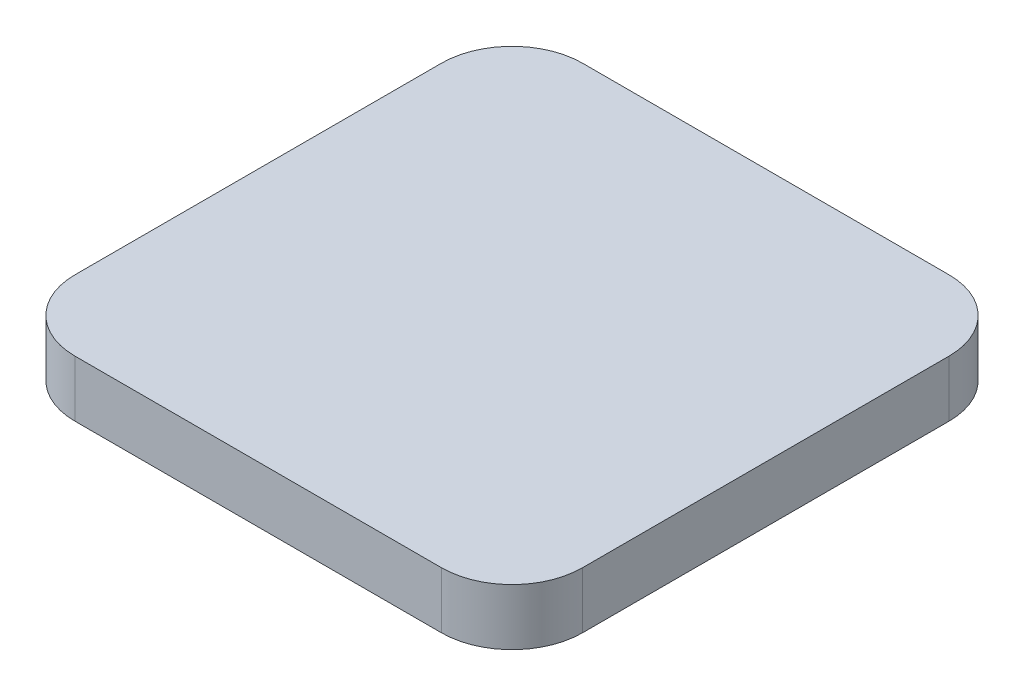
SolidWorks part; units mm, degrees
ref_plane "Front Plane" through (0, 0, 0) normal (0, 0, 1) x (1, 0, 0)
ref_plane "Top Plane" through (0, 0, 0) normal (0, 1, 0) x (1, 0, 0)
ref_plane "Right Plane" through (0, 0, 0) normal (1, 0, 0) x (0, 0, -1)
sketch "Sketch1" plane through (0, 0, 0) normal (0, 1, 0) x (1, 0, 0)
  line L1 (0, 0) -> (36, 0)
  line L2 (0, 0) -> (0, 36)
  line L3 (0, 36) -> (36, 36)
  line L4 (36, 0) -> (36, 36)
  line L5 (0, 0) -> (36, 36) construction
  line L6 (0, 36) -> (36, 0) construction
  point P4 (18, 18)
  dimension "D1" = 36
  dimension "D2" = 36
extrude "Boss-Extrude1" add sketch "Sketch1" along normal blind 4
fillet "Fillet1" radius 5 4 edges at (36, 2, -36) (0, 2, -36) (0, 2, 0) (36, 2, 0)
